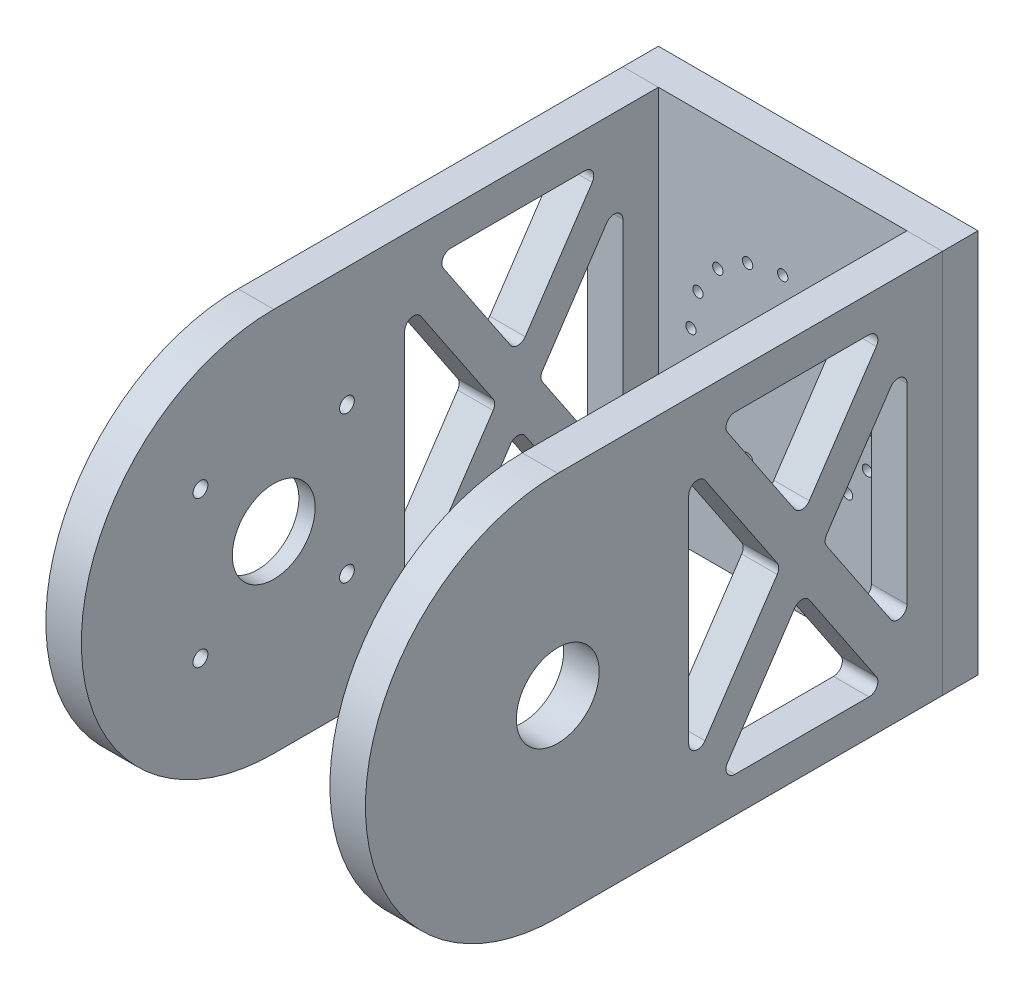
SolidWorks part; units mm, degrees
material "6061 Alloy"
ref_plane "Front Plane" through (0, 0, 0) normal (1, 0, 0) x (0, 1, 0)
ref_plane "Top Plane" through (0, 0, 0) normal (0, 0, 1) x (0, 1, 0)
ref_plane "Right Plane" through (0, 0, 0) normal (0, 1, 0) x (-1, 0, 0)
sketch "Sketch1" plane through (0, 0, 0) normal (1, 0, 0) x (0, 1, 0)
  line L0 (-65, 0) -> (-14, 0) construction
  line L1 (-14, 0) -> (14, 0)
  line L2 (-65, 0) -> (-65, -130)
  line L3 (-65, -130) -> (65, -130)
  line L4 (65, 0) -> (65, -130)
  line L5 (-65, 0) -> (65, -130) construction
  line L6 (-65, -130) -> (65, 0) construction
  line L7 (14, 0) -> (65, 0) construction
  circle A0 centre (0, 0) radius 14
  arc A1 (65, 0) -> (-65, 0) centre (0, 0) ccw
  arc A2 (-65, 0) -> (0, -65) centre (0, 0) ccw construction
  arc A3 (0, -65) -> (65, 0) centre (0, 0) ccw construction
  point P8 (0, -65)
  dimension "D1" = 28
  dimension "D2" = 130
  dimension "D3" = 130
extrude "Boss-Extrude1" add sketch "Sketch1" along normal blind 12 contours L4 A1 L2 L3 A0
sketch "Sketch2" plane through (0, 0, 0) normal (1, 0, 0) x (0, 1, 0)
  line L1 (-65, -130) -> (65, -130)
  line L2 (-65, -130) -> (-65, -142)
  line L3 (-65, -142) -> (65, -142)
  line L4 (65, -130) -> (65, -142)
  line L5 (-65, -130) -> (65, -142) construction
  line L6 (-65, -142) -> (65, -130) construction
  point P4 (0, -136)
  dimension "D1" = 12
extrude "Boss-Extrude2" add sketch "Sketch2" along normal blind 108 separate body
ref_plane "Plane1" through (54, 0, 0) normal (1, 0, 0) x (0, 0, -1)
mirror "Mirror1" about plane through (54, 0, 0) normal (1, 0, 0) of bodies 101
sketch "Sketch3" plane through (108, 0, 0) normal (1, 0, 0) x (0, 1, 0)
  line L1 (-35, 35) -> (35, 35)
  line L2 (-35, 35) -> (-35, -35)
  line L3 (-35, -35) -> (35, -35)
  line L4 (35, 35) -> (35, -35)
  line L5 (-35, 35) -> (35, -35) construction
  line L6 (-35, -35) -> (35, 35) construction
  point P0 (0, 0)
  dimension "D1" = 70
extrude "Cut-Extrude1" cut sketch "Sketch3" along normal blind 3 from surface at -108 starting at face at (0, 0, -14)
sketch "Sketch4" plane through (0, 0, 0) normal (-1, 0, 0) x (0, -1, 0)
  line L0 (0, 0) -> (-24.7487, 24.7487) construction
  line L1 (59.4, 0) -> (-59.4, 0) construction
  circle A0 centre (0, 0) radius 35 construction
  circle A1 centre (-24.7487, 24.7487) radius 2.5
  circle A2 centre (24.7487, 24.7487) radius 2.5
  circle A3 centre (24.7487, -24.7487) radius 2.5
  circle A4 centre (-24.7487, -24.7487) radius 2.5
  point P16 (0, 0)
  dimension "D1" = 70
  dimension "D3" = 5
  dimension "D2" = 45
  dimension "D4" = 4
extrude "Cut-Extrude2" cut sketch "Sketch4" against normal blind 25
sketch "Sketch5" plane through (3, 0, 0) normal (-1, 0, 0) x (0, -1, 0)
  circle A0 centre (0, 0) radius 25
  dimension "D1" = 50
extrude "Cut-Extrude3" cut sketch "Sketch5" against normal blind 3.5
fillet "Fillet1" radius 6 4 edges at (1.5, 35, 35) (1.5, 35, -35) (1.5, -35, -35) (1.5, -35, 35)
sketch "Sketch6" plane through (0, 0, -142) normal (0, 0, -1) x (1, 0, 0)
  line L0 (-59.4, 0) -> (59.4, 0) construction
  line L1 (54, -6.6) -> (54, 6.6) construction
  circle A0 centre (54, 0) radius 35
  dimension "D1" = 70
extrude "Cut-Extrude4" [suppressed] cut sketch "Sketch6" against normal blind 3
sketch "Sketch7" plane through (0, 0, -142) normal (0, 0, -1) x (1, 0, 0)
  line L0 (54, -6.6) -> (54, 6.6) construction
  line L1 (-59.4, 0) -> (59.4, 0) construction
  circle A0 centre (54, 0) radius 31 construction
  circle A1 centre (54, 31) radius 1.75
  circle A2 centre (65.8632, 28.6403) radius 1.75
  circle A3 centre (75.9203, 21.9203) radius 1.75
  circle A4 centre (82.6403, 11.8632) radius 1.75
  circle A5 centre (85, 0) radius 1.75
  circle A6 centre (82.6403, -11.8632) radius 1.75
  circle A7 centre (75.9203, -21.9203) radius 1.75
  circle A8 centre (65.8632, -28.6403) radius 1.75
  circle A9 centre (54, -31) radius 1.75
  circle A10 centre (42.1368, -28.6403) radius 1.75
  circle A11 centre (32.0797, -21.9203) radius 1.75
  circle A12 centre (25.3597, -11.8632) radius 1.75
  circle A13 centre (23, 0) radius 1.75
  circle A14 centre (25.3597, 11.8632) radius 1.75
  circle A15 centre (32.0797, 21.9203) radius 1.75
  circle A16 centre (42.1368, 28.6403) radius 1.75
  dimension "D1" = 62
  dimension "D2" = 3.5
  dimension "D3" = 16
extrude "Cut-Extrude5" cut sketch "Sketch7" against normal blind 65
sketch "Sketch8" plane through (0, 0, 0) normal (-1, 0, 0) x (0, -1, 0)
  line L0 (0, -35) -> (0, -130) construction
  line L1 (29, -35) -> (-29, -35) construction
  line L2 (0, 59.4) -> (0, -59.4) construction
  line L3 (-65, -130) -> (65, -130) construction
  line L4 (-65, 0) -> (-65, -130) construction
  line L5 (-36.4523, -44.2515) -> (36.4523, -44.2515)
  line L6 (-53, -59.8418) -> (-53, -105.1582)
  line L7 (-32.3488, -118) -> (32.3488, -118)
  line L8 (53, -59.8418) -> (53, -105.1582)
  line L9 (-53, -47) -> (53, -118) construction
  line L10 (-53, -118) -> (53, -47) construction
  line L11 (-48.3305, -57.3493) -> (-14.5028, -80.0075)
  line L12 (-48.3305, -107.6507) -> (-14.5028, -84.9925)
  line L13 (-34.0184, -112.5075) -> (-1.6695, -90.8399)
  line L15 (48.3305, -107.6507) -> (14.5028, -84.9925)
  line L16 (14.5028, -80.0075) -> (48.3305, -57.3493)
  line L17 (1.6695, -74.1601) -> (38.1218, -49.744)
  line L18 (1.6695, -90.8399) -> (34.0184, -112.5075)
  line L19 (-1.6695, -74.1601) -> (-38.1218, -49.744)
  arc A0 (1.6695, -74.1601) -> (-1.6695, -74.1601) centre (0, -71.6676) cw
  arc A1 (-1.6695, -90.8399) -> (1.6695, -90.8399) centre (0, -93.3324) cw
  arc A2 (32.3488, -118) -> (34.0184, -112.5075) centre (32.3488, -115) ccw
  arc A3 (-34.0184, -112.5075) -> (-32.3488, -118) centre (-32.3488, -115) ccw
  arc A4 (-48.3305, -107.6507) -> (-53, -105.1582) centre (-50, -105.1582) cw
  arc A5 (-48.3305, -57.3493) -> (-53, -59.8418) centre (-50, -59.8418) ccw
  arc A6 (-14.5028, -84.9925) -> (-14.5028, -80.0075) centre (-16.1723, -82.5) ccw
  arc A7 (14.5028, -80.0075) -> (14.5028, -84.9925) centre (16.1723, -82.5) ccw
  arc A8 (48.3305, -107.6507) -> (53, -105.1582) centre (50, -105.1582) ccw
  arc A9 (36.4523, -44.2515) -> (38.1218, -49.744) centre (36.4523, -47.2515) cw
  arc A10 (-36.4523, -44.2515) -> (-38.1218, -49.744) centre (-36.4523, -47.2515) ccw
  arc A11 (48.3305, -57.3493) -> (53, -59.8418) centre (50, -59.8418) cw
  point P7 (0, -82.5)
  point P31 (0, -75.2784)
  point P34 (0, -89.7216)
  point P51 (46.3219, -44.2515)
  point P56 (53, -54.2216)
  dimension "D4" = 3
  dimension "D5" = 3
  dimension "D1" = 12
  dimension "D2" = 12
  dimension "D3" = 12
extrude "Cut-Extrude6" cut sketch "Sketch8" against normal through all both and the other way through all
